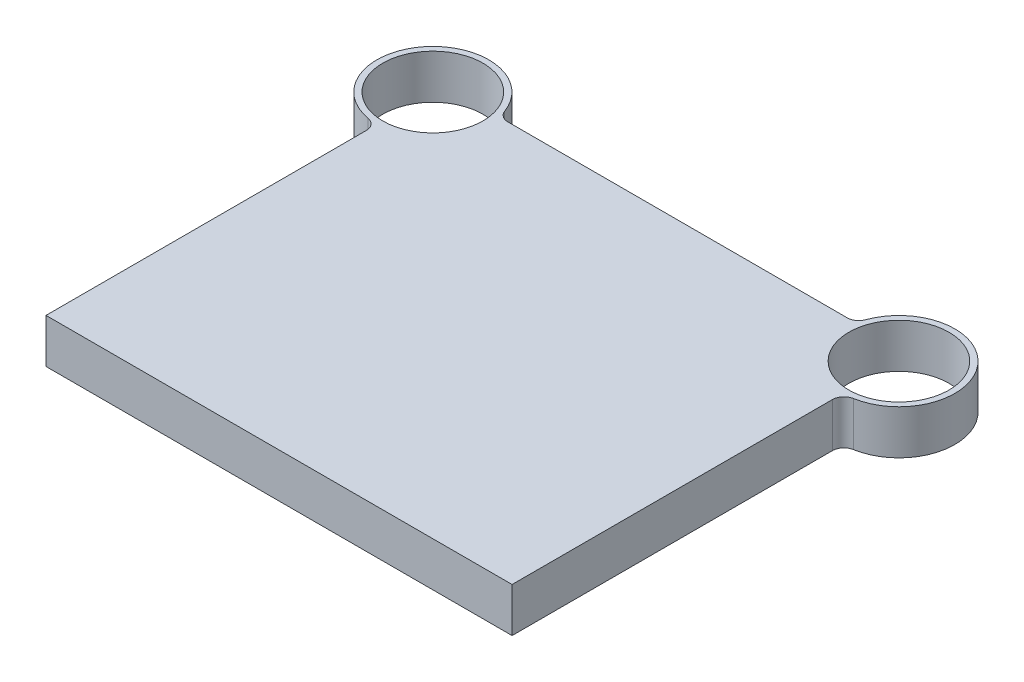
SolidWorks part; units mm, degrees
ref_plane "Front Plane" through (0, 0, 0) normal (0, 0, 1) x (1, 0, 0)
ref_plane "Top Plane" through (0, 0, 0) normal (0, 1, 0) x (1, 0, 0)
ref_plane "Right Plane" through (0, 0, 0) normal (1, 0, 0) x (0, 0, -1)
sketch "Sketch1" plane through (0, 0, 0) normal (0, 1, 0) x (1, 0, 0)
  line L0 (200, 0) -> (-200, 0)
  line L1 (-200, 0) -> (-200, 284)
  line L2 (0, 0) -> (0, 342) construction
  line L3 (153.0532, 342) -> (-153.0532, 342)
  line L4 (200, 0) -> (200, 284)
  arc A0 (-153.0532, 342) -> (-200, 284) centre (-200, 332) ccw
  circle A1 centre (-200, 332) radius 43
  circle A2 centre (200, 332) radius 43
  arc A3 (153.0532, 342) -> (200, 284) centre (200, 332) cw
  point P9 (-245.0149, 304.081)
  point P10 (-268.3497, 245.8719)
  point P11 (-195.0653, 342)
  dimension "D3" = 96
  dimension "D4" = 86
  dimension "D1" = 342
  dimension "D2" = 332
  dimension "D5" = 400
  dimension "D6" = 400
extrude "Boss-Extrude1" add sketch "Sketch1" along normal blind 38
fillet "Fillet1" radius 10 4 edges at (-200, 19, -284) (200, 19, -284) (153.0532, 19, -342) (-153.0532, 19, -342)
